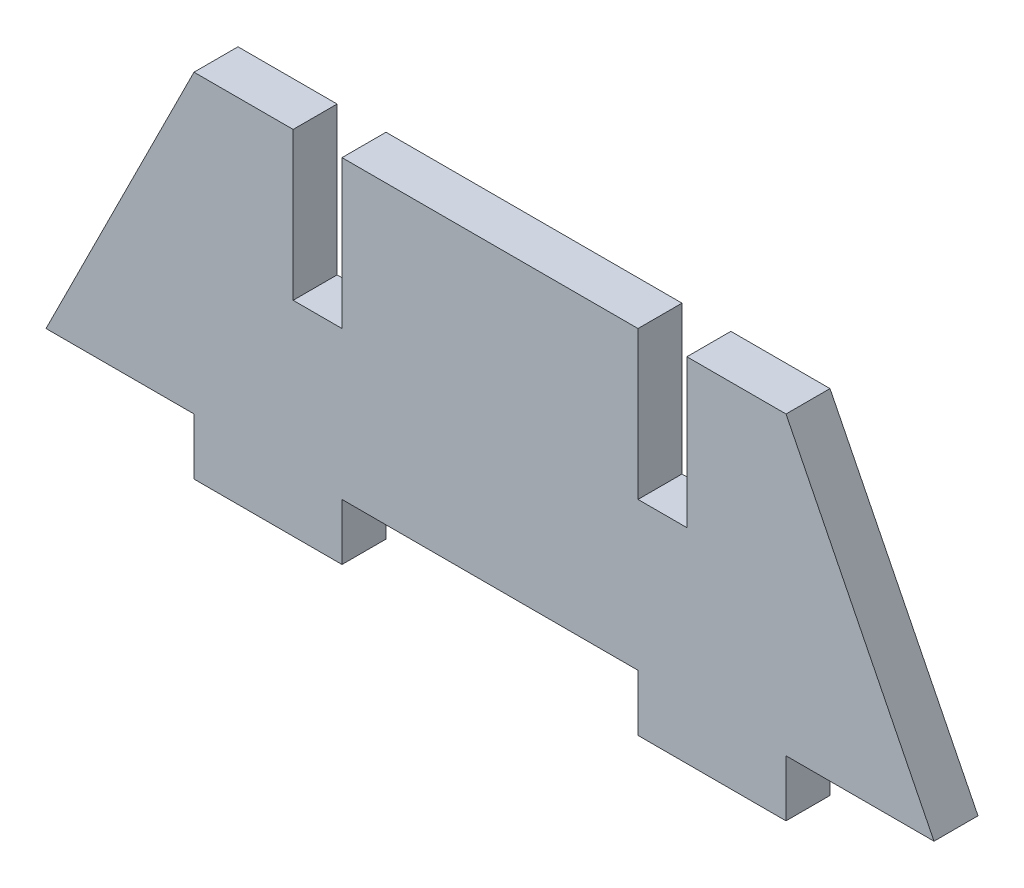
SolidWorks part; units mm, degrees
ref_plane "Front Plane" through (0, 0, 0) normal (0, 0, 1) x (1, 0, 0)
ref_plane "Top Plane" through (0, 0, 0) normal (0, 1, 0) x (1, 0, 0)
ref_plane "Right Plane" through (0, 0, 0) normal (1, 0, 0) x (0, 0, -1)
sketch "Sketch1" plane through (0, 0, 0) normal (0, 0, 1) x (1, 0, 0)
  line L1 (-20, -10) -> (20, -10)
  line L2 (-20, -10) -> (-20, 10)
  line L3 (-20, 10) -> (20, 10)
  line L4 (20, -10) -> (20, 10)
  line L5 (-20, -10) -> (20, 10) construction
  line L6 (-20, 10) -> (20, -10) construction
  point P0 (0, 0)
  dimension "D1" = 40
  dimension "D2" = 20
extrude "Boss-Extrude1" add sketch "Sketch1" along normal blind 2.9718
sketch "Sketch2" plane through (0, 0, 2.9718) normal (0, 0, 1) x (1, 0, 0)
  line L0 (-20, 10) -> (-30, -10)
  line L1 (-30, -10) -> (-20, -10)
  line L2 (-20, -10) -> (-20, 10)
  line L3 (0, 0) -> (0, -4.3451) construction
  line L4 (20, -10) -> (20, 10)
  line L5 (20, 10) -> (30, -10)
  line L6 (30, -10) -> (20, -10)
  dimension "D1" = 10
extrude "Boss-Extrude2" add sketch "Sketch2" against normal blind 2.9718
sketch "Sketch3" plane through (0, 0, 2.9718) normal (0, 0, 1) x (1, 0, 0)
  line L0 (20, 10) -> (-20, 10) construction
  line L1 (-13.302, 20) -> (-10, 20)
  line L2 (-13.302, 20) -> (-13.302, 0)
  line L3 (-13.302, 0) -> (-10, 0)
  line L4 (-10, 20) -> (-10, 0)
  line L5 (-13.302, 20) -> (-10, 0) construction
  line L6 (-13.302, 0) -> (-10, 20) construction
  line L7 (0, 0) -> (0, 4.7702) construction
  line L8 (10, 20) -> (10, 0)
  line L9 (13.302, 0) -> (10, 0)
  line L10 (13.302, 20) -> (13.302, 0)
  line L11 (13.302, 20) -> (10, 20)
  point P0 (-11.651, 10)
  dimension "D1" = 20
  dimension "D2" = 3.302
  dimension "D3" = 10
extrude "Cut-Extrude1" cut sketch "Sketch3" against normal through all
sketch "Sketch4" plane through (0, 0, 2.9718) normal (0, 0, 1) x (1, 0, 0)
  line L0 (-30, -10) -> (30, -10) construction
  line L1 (-20, -10) -> (-10, -10)
  line L2 (-20, -10) -> (-20, -13.81)
  line L3 (-20, -13.81) -> (-10, -13.81)
  line L4 (-10, -10) -> (-10, -13.81)
  line L5 (0, 0) -> (0, -2.9858) construction
  line L6 (10, -10) -> (10, -13.81)
  line L7 (20, -13.81) -> (10, -13.81)
  line L8 (20, -10) -> (20, -13.81)
  line L9 (20, -10) -> (10, -10)
  dimension "D1" = 10
  dimension "D2" = 3.81
extrude "Boss-Extrude3" add sketch "Sketch4" against normal blind 2.9718
